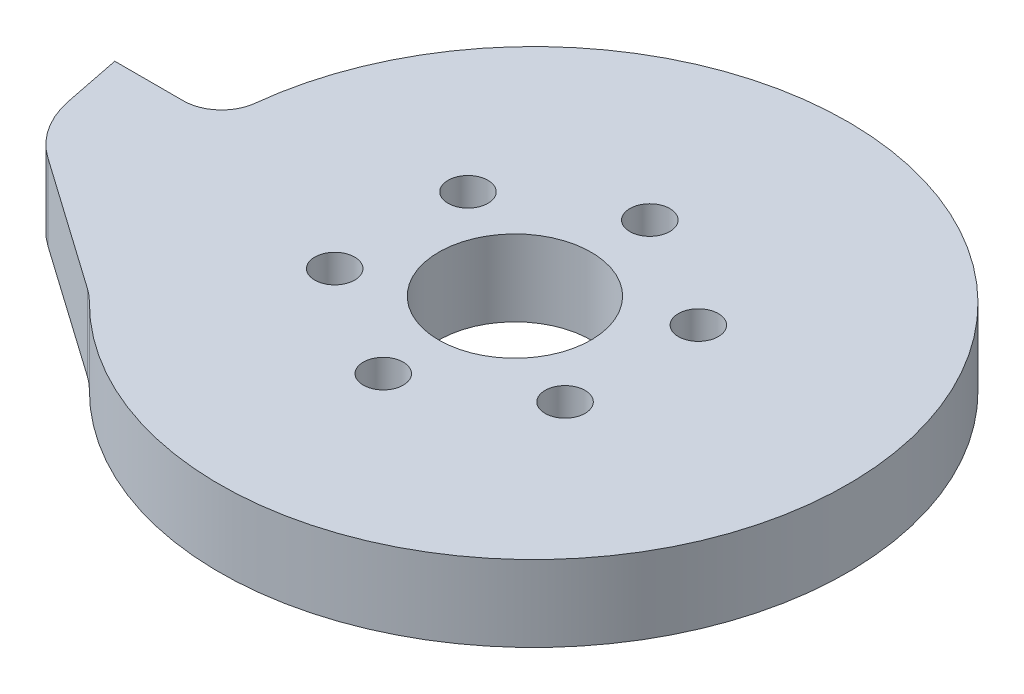
SolidWorks part; units mm, degrees
material "Plain Carbon Steel"
ref_plane "Front Plane" through (0, 0, 0) normal (0, 0, 1) x (1, 0, 0)
ref_plane "Top Plane" through (0, 0, 0) normal (0, 1, 0) x (1, 0, 0)
ref_plane "Right Plane" through (0, 0, 0) normal (1, 0, 0) x (0, 0, -1)
sketch "Sketch1" plane through (0, 0, 0) normal (0, 1, 0) x (1, 0, 0)
  line L0 (-33, 0) -> (-44, 0)
  line L1 (-44, 0) -> (-42, -10)
  line L2 (-42, -10) -> (-24, -22.6495)
  arc A2 (-33, 0) -> (-24, -22.6495) centre (0, 0) cw
  circle A3 centre (-1.62, -0.35) radius 8
  dimension "D1" = 33
  dimension "D2" = 11
  dimension "D8" = 16
  dimension "D3" = 10
  dimension "D4" = 2
  dimension "D5" = 18
  dimension "D6" = 1.62
  dimension "D7" = 0.35
extrude "Boss-Extrude1" add sketch "Sketch1" along normal blind 8
fillet "Fillet1" radius 4 1 edges at (-33, 4, 0)
fillet "Fillet2" radius 10 2 edges at (-24, 4, 22.6495) (-42, 4, 10)
sketch "Sketch2" plane through (0, 8, 0) normal (0, 1, 0) x (1, 0, 0)
  circle A0 centre (-1.4524, 13.649) radius 2.1
  circle A1 centre (-1.62, -0.35) radius 8 construction
  circle A2 centre (10.6509, 6.6441) radius 2.1
  circle A3 centre (10.6362, -7.3401) radius 2.1
  circle A4 centre (-1.4819, -14.3194) radius 2.1
  circle A5 centre (-13.5851, -7.3145) radius 2.1
  circle A6 centre (-13.5704, 6.6697) radius 2.1
  point P17 (-1.4671, -0.3352)
  dimension "D2" = 4.2
  dimension "D1" = 14
  dimension "D3" = 6
extrude "Cut-Extrude1" cut sketch "Sketch2" against normal through all
